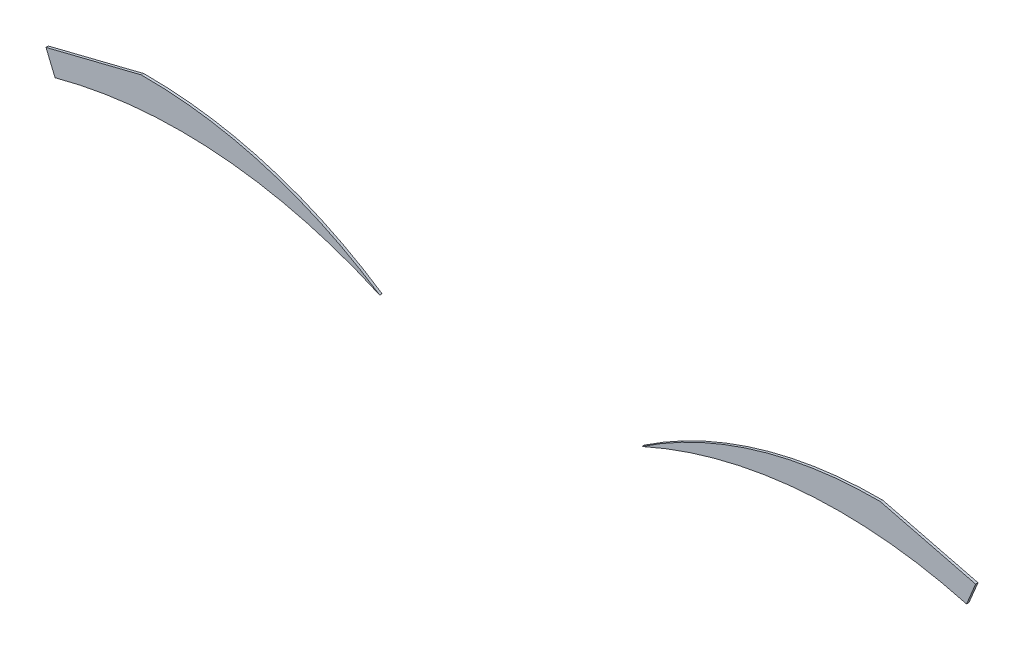
SolidWorks part; units mm, degrees
ref_plane "Alzado" through (0, 0, 0) normal (0, 0, 1) x (1, 0, 0)
ref_plane "Planta" through (0, 0, 0) normal (0, 1, 0) x (1, 0, 0)
ref_plane "Vista lateral" through (0, 0, 0) normal (1, 0, 0) x (0, 0, -1)
sketch "Model" plane through (0, 0, 0) normal (0, 0, 1) x (1, 0, 0)
  line L0 (30.8791, 32.5865) -> (30.4987, 33.4998)
  line L1 (30.4987, 33.4998) -> (34.4987, 34.4998)
  line L2 (65.5013, 34.4998) -> (69.5013, 33.4998)
  line L3 (69.5013, 33.4998) -> (69.1209, 32.5865)
  arc A0 (44.4987, 31.4998) -> (30.8791, 32.5865) centre (36.1773, 13.0995) ccw
  arc A1 (44.4987, 31.4998) -> (34.4987, 34.4998) centre (34.6237, 16.7498) ccw
  arc A2 (69.1209, 32.5865) -> (55.5013, 31.4998) centre (63.8227, 13.0995) ccw
  arc A3 (65.5013, 34.4998) -> (55.5013, 31.4998) centre (65.3763, 16.7498) ccw
extrude "Saliente-Extruir1" add sketch "Model" along normal blind 0.1
